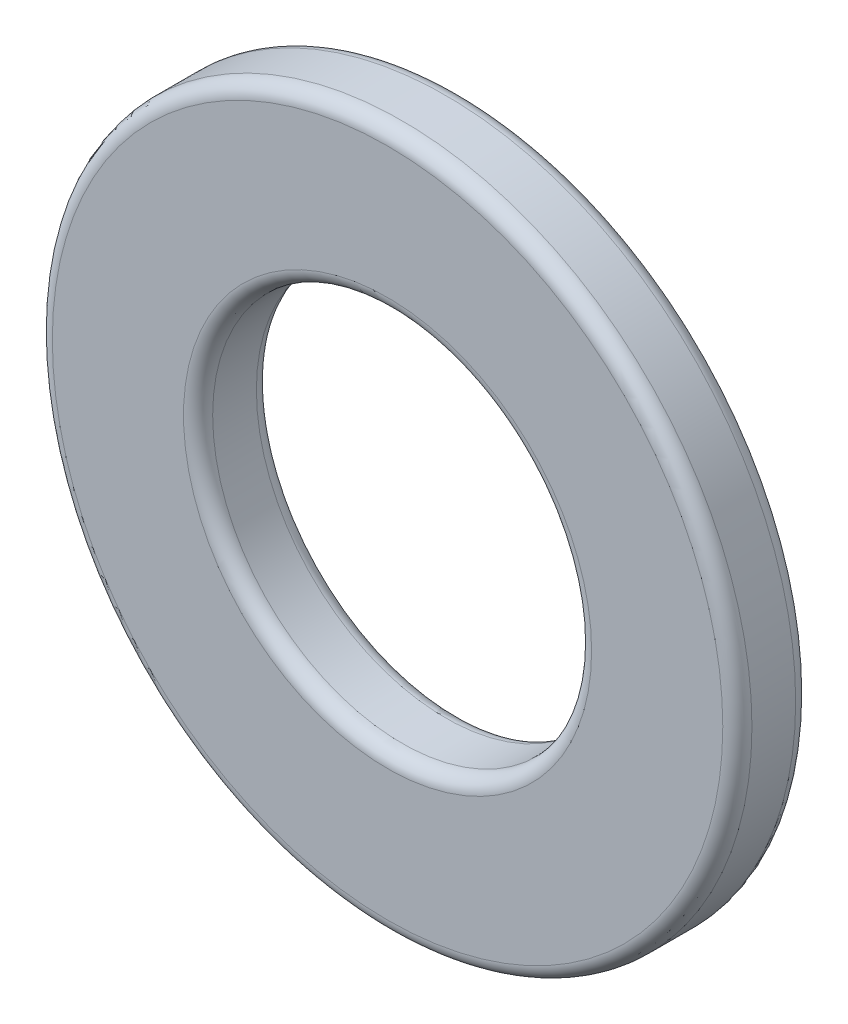
SolidWorks part; units mm, degrees
ref_plane "Front Plane" through (0, 0, 0) normal (0, 0, 1) x (1, 0, 0)
ref_plane "Top Plane" through (0, 0, 0) normal (0, 1, 0) x (1, 0, 0)
ref_plane "Right Plane" through (0, 0, 0) normal (1, 0, 0) x (0, 0, -1)
sketch "Sketch1" plane through (0, 0, 0) normal (0, 0, 1) x (1, 0, 0)
  circle A0 centre (0, 0) radius 6.5
  circle A1 centre (0, 0) radius 12
  dimension "D1" = 13
  dimension "D2" = 24
extrude "Boss-Extrude1" add sketch "Sketch1" along normal blind 2.5
fillet "Fillet1" radius 0.5 4 edges at (6.5, 0, 0) (12, 0, 0) (12, 0, 2.5) (6.5, 0, 2.5)
